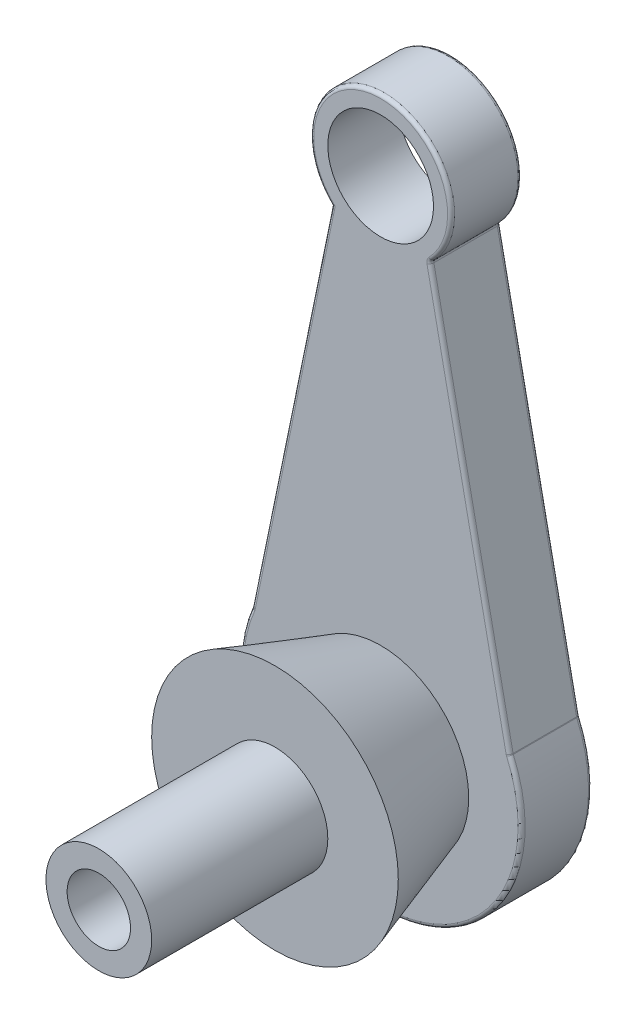
SolidWorks part; units mm, degrees
material "ABS"
ref_plane "Front Plane" through (0, 0, 0) normal (0, 0, 1) x (1, 0, 0)
ref_plane "Top Plane" through (0, 0, 0) normal (0, 1, 0) x (1, 0, 0)
ref_plane "Right Plane" through (0, 0, 0) normal (1, 0, 0) x (0, 0, -1)
sketch "Sketch10" plane through (0, 0, 0) normal (0, 0, 1) x (1, 0, 0)
  line L0 (0, 3.3637) -> (0, -17.5362) construction
  line L1 (-7, 12.658) -> (-18.3046, -42.342)
  line L2 (7, 12.658) -> (18.3046, -42.342)
  arc A0 (-7, 12.658) -> (7, 12.658) centre (0, 19.7995) cw
  arc A1 (18.3046, -42.342) -> (-18.3046, -42.342) centre (0, -50.4005) cw
  dimension "D1" = 10
  dimension "D2" = 20
  dimension "D3" = 55
  dimension "D4" = 70.2
  dimension "D5" = 7
  dimension "D6" = 12.658
extrude "Boss-Extrude2" add sketch "Sketch10" against normal blind 10
sketch "Sketch11" plane through (0, 0, 0) normal (0, 0, 1) x (1, 0, 0)
  circle A0 centre (0, 19.7995) radius 7.5
  dimension "D1" = 15
extrude "Cut-Extrude1" cut sketch "Sketch11" against normal through all
sketch "Sketch12" plane through (0, 0, 0) normal (0, 0, 1) x (1, 0, 0)
  circle A0 centre (0, -50.4005) radius 12.5
  dimension "D1" = 25
ref_plane "Plane1" through (0, 0, 15) normal (0, 0, 1) x (1, 0, 0)
sketch "Sketch13" plane through (0, 0, 15) normal (0, 0, 1) x (1, 0, 0)
  circle A0 centre (0, -50.4005) radius 17.5
  dimension "D1" = 35
loft "Loft1" add profiles "Sketch12", "Sketch13"
sketch "Sketch16" plane through (0, 0, 15) normal (0, 0, 1) x (1, 0, 0)
  circle A0 centre (0, -50.4005) radius 7.5
  dimension "D1" = 15
extrude "Boss-Extrude3" add sketch "Sketch16" along normal blind 25
sketch "Sketch17" plane through (0, 0, -10) normal (0, 0, -1) x (-1, 0, 0)
  circle A0 centre (0, -50.4005) radius 13
extrude "Cut-Extrude2" cut sketch "Sketch17" against normal blind 7.7
fillet "Fillet2" radius 0.5 11 edges at (0, 29.7995, -10) (0, 29.7995, 0) (0, -70.4005, -10) (-18.3046, -42.342, -5) (0, -70.4005, 0) (7, 12.658, -5) (12.6523, -14.842, -10) (18.3046, -42.342, -5) (12.6523, -14.842, 0) (-12.6523, -14.842, -10) (-12.6523, -14.842, 0)
sketch "Sketch18" plane through (0, 0, -2.3) normal (0, 0, -1) x (-1, 0, 0)
  circle A0 centre (0, -50.4005) radius 4.5
  dimension "D1" = 9
extrude "Cut-Extrude3" cut sketch "Sketch18" against normal up to next
